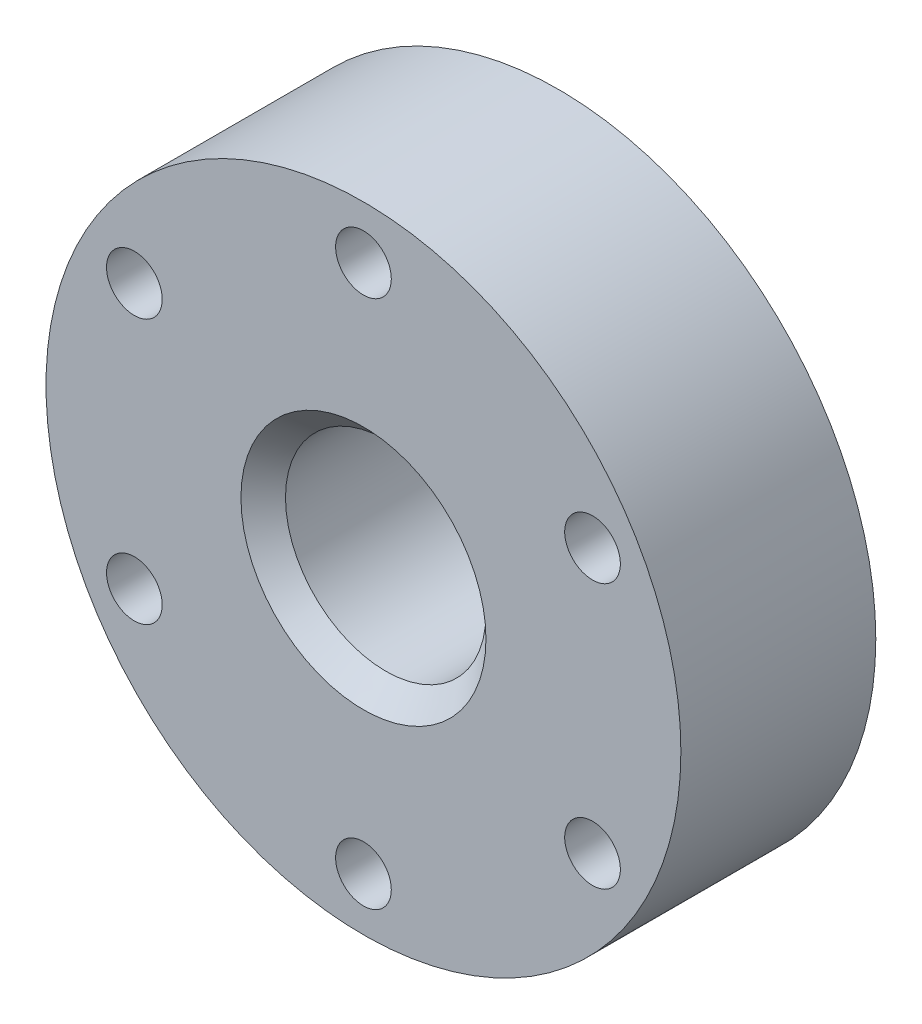
SolidWorks part; units mm, degrees
other "攝影機1"
material "尼龍 101"
ref_plane "Front Plane" through (0, 0, 0) normal (0, 0, 1) x (1, 0, 0)
ref_plane "Top Plane" through (0, 0, 0) normal (0, 1, 0) x (1, 0, 0)
ref_plane "Right Plane" through (0, 0, 0) normal (1, 0, 0) x (0, 0, -1)
sketch "Sketch1" plane through (0, 0, 0) normal (0, 0, 1) x (1, 0, 0)
  circle A0 centre (0, 0) radius 28.5
  circle A1 centre (0, 0) radius 23.75 construction
  circle A2 centre (0, 23.75) radius 2.5
  circle A3 centre (20.5681, 11.875) radius 2.5
  circle A4 centre (20.5681, -11.875) radius 2.5
  circle A5 centre (0, -23.75) radius 2.5
  circle A6 centre (-20.5681, -11.875) radius 2.5
  circle A7 centre (-20.5681, 11.875) radius 2.5
  point P18 (0, 0)
  dimension "D1" = 57
  dimension "D2" = 47.5
  dimension "D3" = 5
extrude "Boss-Extrude1" add sketch "Sketch1" along normal blind 17.5
sketch "Sketch2" plane through (0, 0, 17.5) normal (0, 0, 1) x (1, 0, 0)
  circle A0 centre (0, 0) radius 9
  dimension "D1" = 18
extrude "Cut-Extrude1" cut sketch "Sketch2" against normal through all
chamfer "Chamfer1" distance 2 angle 45 2 edges at (9, 0, 0) (9, 0, 17.5)
